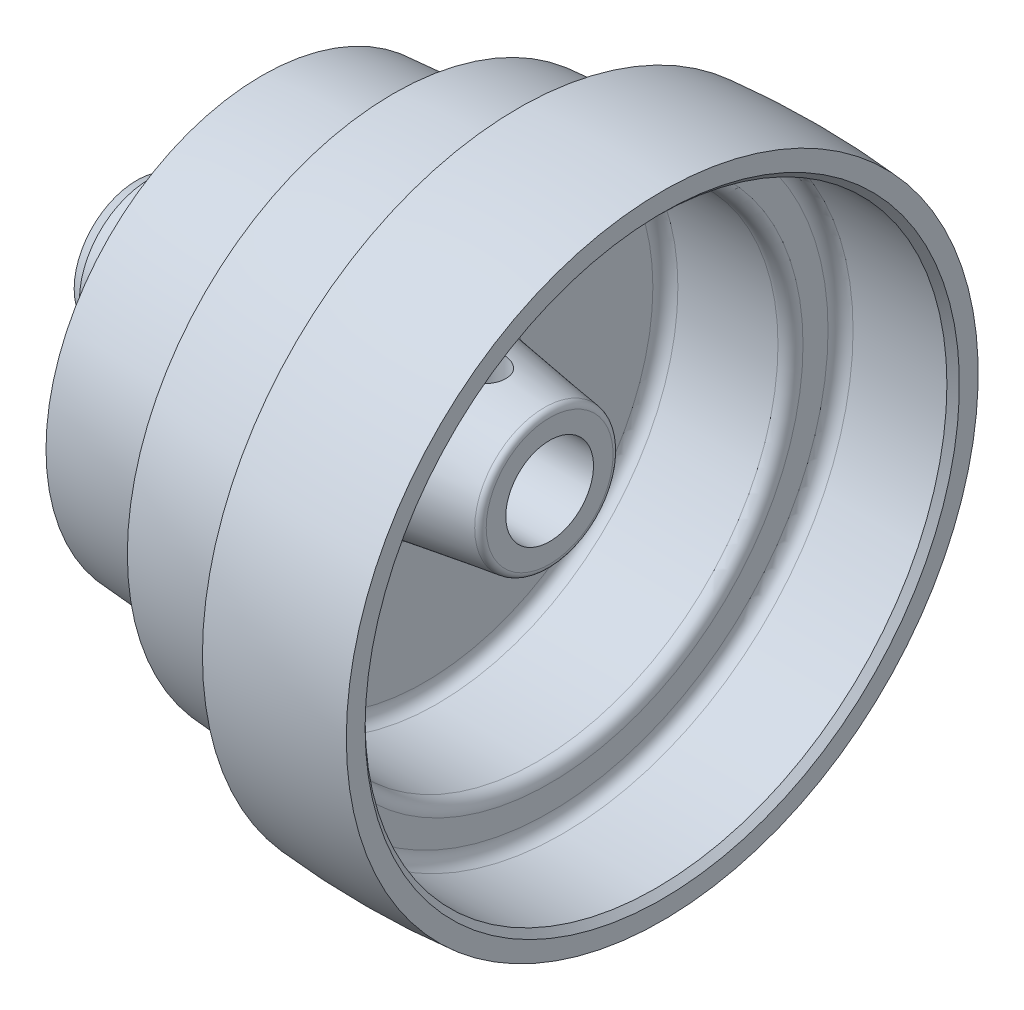
SolidWorks part; units mm, degrees
ref_plane "Front Plane" through (0, 0, 0) normal (0, 0, 1) x (1, 0, 0)
ref_plane "Top Plane" through (0, 0, 0) normal (0, 1, 0) x (1, 0, 0)
ref_plane "Right Plane" through (0, 0, 0) normal (1, 0, 0) x (0, 0, -1)
sketch "Sketch1" plane through (0, 0, 0) normal (0, 0, 1) x (1, 0, 0)
  line L0 (0, 0) -> (133.35, 0) construction
  line L1 (0, 11.1252) -> (0, 15.875)
  line L2 (3.1601, 17.6995) -> (60.5625, 22.0047)
  line L3 (63.5, 25.1708) -> (63.5, 46.8312)
  line L4 (60.325, 50.0063) -> (33.3375, 50.0062)
  line L5 (31.75, 51.5938) -> (31.75, 54.7687)
  line L6 (0, 15.875) -> (3.1601, 17.6995)
  line L7 (73.025, 24.9593) -> (73.025, 57.9437)
  line L8 (75.729, 21.8194) -> (103.423, 17.6653)
  line L9 (104.775, 16.0954) -> (104.775, 11.1252)
  line L10 (104.775, 11.1252) -> (0, 11.1252)
  line L11 (65.0875, 67.4688) -> (65.0875, 54.7687)
  line L12 (76.2, 61.1187) -> (101.6, 61.1187)
  line L13 (104.775, 64.2938) -> (104.775, 70.6437)
  line L14 (107.95, 73.8188) -> (131.7625, 73.8188)
  line L15 (96.8375, 67.4688) -> (96.8375, 80.1688)
  line L16 (133.35, 75.4063) -> (133.35, 80.1688)
  line L17 (131.7625, 73.8188) -> (133.35, 75.4063)
  arc A0 (31.75, 54.7687) -> (65.0875, 54.7687) centre (48.4187, -119.8562) cw
  arc A1 (65.0875, 67.4688) -> (96.8375, 67.4688) centre (80.9625, -90.8844) cw
  arc A2 (96.8375, 80.1688) -> (133.35, 80.1688) centre (115.0938, -129.3813) cw
  arc A3 (104.775, 70.6437) -> (107.95, 73.8188) centre (107.95, 70.6438) cw
  arc A4 (101.6, 61.1187) -> (104.775, 64.2938) centre (101.6, 64.2938) ccw
  arc A5 (73.025, 57.9437) -> (76.2, 61.1187) centre (76.2, 57.9438) cw
  arc A6 (63.5, 46.8312) -> (60.325, 50.0063) centre (60.325, 46.8313) ccw
  arc A7 (60.5625, 22.0047) -> (63.5, 25.1708) centre (60.325, 25.1708) ccw
  arc A8 (73.025, 24.9593) -> (75.729, 21.8194) centre (76.2, 24.9593) ccw
  arc A9 (33.3375, 50.0062) -> (31.75, 51.5938) centre (33.3375, 51.5937) cw
  arc A11 (103.423, 17.6653) -> (104.775, 16.0954) centre (103.1875, 16.0954) cw
  point P3 (0, 17.4625)
  point P20 (104.775, 16.2251)
  point P30 (104.775, 61.1187)
  point P33 (73.025, 61.1187)
  point P38 (63.5, 22.225)
  point P41 (73.025, 22.225)
  point P44 (31.75, 50.0062)
  point P46 (133.35, 73.8188)
  point P47 (133.35, 73.8188)
  point P50 (104.775, 17.4625)
  dimension "D16" = 0.7937
  dimension "D21" = 0.7937
  dimension "D24" = 0.7937
  dimension "D25" = 3.175
  dimension "D26" = 1.5875
  dimension "D1" = 133.35
  dimension "D2" = 22.225
  dimension "D3" = 17.4625
  dimension "D4" = 1.5875
  dimension "D5" = 60
  dimension "D6" = 63.5
  dimension "D7" = 50.0062
  dimension "D8" = 22.225
  dimension "D9" = 9.525
  dimension "D10" = 17.4625
  dimension "D11" = 31.75
  dimension "D12" = 11.1252
  dimension "D13" = 54.7687
  dimension "D14" = 101.6
  dimension "D15" = 33.3375
  dimension "D17" = 67.4688
  dimension "D18" = 61.1187
  dimension "D19" = 31.75
  dimension "D20" = 7.9375
  dimension "D22" = 80.1688
  dimension "D23" = 73.8188
  dimension "D27" = 1.5875
  dimension "D28" = 45
  dimension "D29" = 1.5875
revolve "Revolve1" add sketch "Sketch1" angle 360 about L0
sketch "Sketch2" plane through (0, 0, 0) normal (0, 1, 0) x (1, 0, 0)
  line L0 (133.35, -80.1688) -> (133.35, 80.1688) construction
  circle A0 centre (88.9, 0) radius 4.7625
  dimension "D2" = 9.525
  dimension "D1" = 44.45
extrude "Cut-Extrude1" cut sketch "Sketch2" along normal up to next
